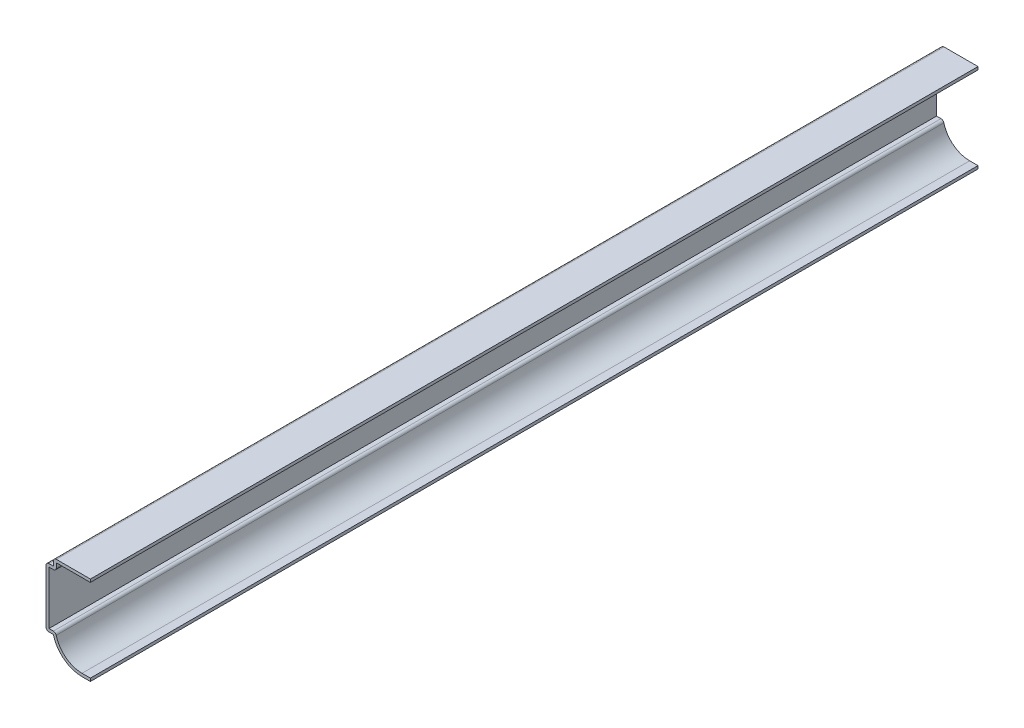
SolidWorks part; units mm, degrees
ref_plane "Front Plane" through (0, 0, 0) normal (0, 0, 1) x (1, 0, 0)
ref_plane "Top Plane" through (0, 0, 0) normal (0, 1, 0) x (1, 0, 0)
ref_plane "Right Plane" through (0, 0, 0) normal (1, 0, 0) x (0, 0, -1)
sketch "Sketch1" plane through (0, 0, 0) normal (0, 0, 1) x (1, 0, 0)
  line L0 (0, 0) -> (-3.5783, 0)
  line L1 (-15.875, 9.525) -> (-19.05, 9.525)
  line L2 (-19.05, 9.525) -> (-19.05, 34.925)
  line L3 (-19.05, 34.925) -> (-15.875, 34.925)
  line L4 (-15.875, 34.925) -> (-15.875, 38.1)
  line L5 (-15.875, 38.1) -> (0, 38.1)
  arc A0 (-3.5783, 0) -> (-15.875, 9.525) centre (-3.5783, 12.7) cw
  point P10 (-14.7211, 12.7058)
  point P11 (0, 0)
  dimension "D4" = 12.7
  dimension "D1" = 38.1
  dimension "D2" = 19.05
  dimension "D3" = 19.05
  dimension "D5" = 9.525
  dimension "D6" = 3.175
  dimension "D7" = 3.175
  dimension "D8" = 3.175
extrude "Extrude-Thin1" add sketch "Sketch1" against normal blind 381 thin
fillet "Fillet1" radius 1.27 5 edges at (-14.8484, 10.795, -190.5) (-19.05, 9.525, -190.5) (-14.605, 33.655, -190.5) (-19.05, 34.925, -190.5) (-15.875, 38.1, -190.5)
